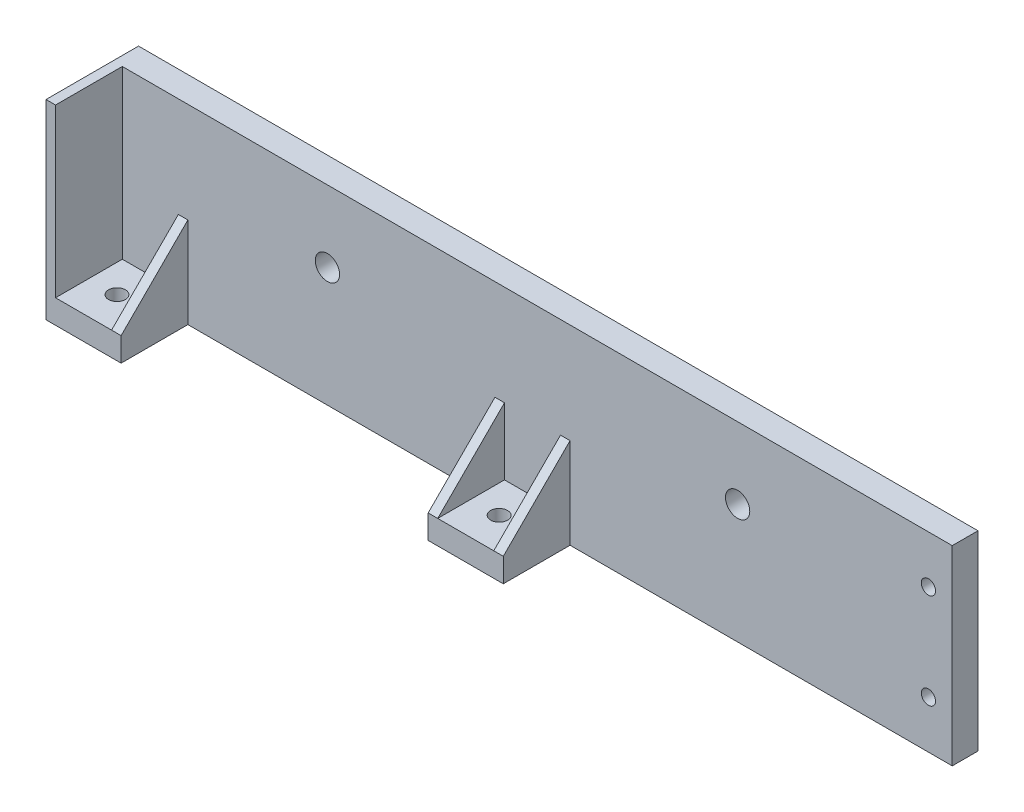
SolidWorks part; units mm, degrees
ref_plane "Front Plane" through (0, 0, 0) normal (0, 0, 1) x (1, 0, 0)
ref_plane "Top Plane" through (0, 0, 0) normal (0, 1, 0) x (1, 0, 0)
ref_plane "Right Plane" through (0, 0, 0) normal (1, 0, 0) x (0, 0, -1)
sketch "Sketch1" plane through (0, 0, 0) normal (0, 0, 1) x (1, 0, 0)
  line L1 (-111.76, -25.4) -> (111.76, -25.4)
  line L2 (-111.76, -25.4) -> (-111.76, 25.4)
  line L3 (-111.76, 25.4) -> (111.76, 25.4)
  line L4 (111.76, -25.4) -> (111.76, 25.4)
  circle A0 centre (-54.61, 6.35) radius 38.1
  circle A1 centre (54.61, 6.35) radius 38.1
  circle A2 centre (-54.61, 6.35) radius 3.2385
  circle A3 centre (54.61, 6.35) radius 3.2385
  point P0 (0, 0)
  dimension "D5" = 76.2
  dimension "D6" = 76.2
  dimension "D7" = 6.477
  dimension "D8" = 6.477
  dimension "D9" = 19.05
  dimension "D3" = 57.15
  dimension "D4" = 57.15
  dimension "D10" = 19.05
  dimension "D1" = 223.52
  dimension "D2" = 50.8
extrude "Boss-Extrude1" add sketch "Sketch1" along normal blind 6.858
sketch "Sketch2" plane through (0, 0, 6.858) normal (0, 0, 1) x (1, 0, 0)
  line L0 (-111.76, -25.4) -> (-91.76, -25.4)
  line L1 (-111.76, -25.4) -> (-111.76, -19.05)
  line L2 (-91.76, -25.4) -> (-91.76, -19.05)
  line L3 (-111.76, -19.05) -> (-91.76, -19.05)
  line L4 (-111.76, -25.4) -> (111.76, -25.4) construction
extrude "Boss-Extrude2" add sketch "Sketch2" along normal blind 17.78
sketch "Sketch3" plane through (0, -19.05, 0) normal (0, 1, 0) x (1, 0, 0)
  circle A0 centre (-101.76, -15.748) radius 2.25
extrude "Cut-Extrude1" cut sketch "Sketch3" against normal blind 17.78
sketch "Sketch4" plane through (0, -19.05, 0) normal (0, 1, 0) x (1, 0, 0)
  line L0 (-111.76, -24.638) -> (-111.76, -6.858)
  line L1 (-111.76, -24.638) -> (-109.22, -24.638)
  line L2 (-111.76, -6.858) -> (-109.22, -6.858)
  line L3 (-109.22, -24.638) -> (-109.22, -6.858)
  line L4 (-91.76, -24.638) -> (-91.76, -6.858)
  line L5 (-91.76, -24.638) -> (-94.3, -24.638)
  line L6 (-91.76, -6.858) -> (-94.3, -6.858)
  line L7 (-94.3, -24.638) -> (-94.3, -6.858)
extrude "Boss-Extrude3" add sketch "Sketch4" along normal blind 17.78
sketch "Sketch6" plane through (-111.76, 0, 0) normal (-1, 0, 0) x (0, 0, 1)
  line L0 (24.638, -1.27) -> (6.858, -1.27)
  line L1 (24.638, -1.27) -> (24.638, -19.05)
  line L4 (24.638, -19.05) -> (6.858, -1.27)
extrude "Cut-Extrude2" cut sketch "Sketch6" against normal up to surface (20 mm away) up to face at (-91.76, -13.335, 15.748)
pattern_linear "LPattern1" count 2 spacing 101.76 along (1, 0, 0) of "Boss-Extrude2", "Cut-Extrude1", "Boss-Extrude3", "Cut-Extrude2"
sketch "Sketch7" plane through (-111.76, 0, 0) normal (-1, 0, 0) x (0, 0, 1)
  line L0 (24.638, -19.05) -> (24.638, 25.4)
  line L1 (6.858, 25.4) -> (24.638, 25.4)
  line L2 (6.858, 25.4) -> (6.858, -1.27)
  line L3 (6.858, -1.27) -> (24.638, -19.05)
extrude "Boss-Extrude4" add sketch "Sketch7" against normal up to surface (2.54 mm away) up to face at (-109.22, -13.1233, 12.7847)
sketch "Sketch8" plane through (0, 0, 0) normal (0, 0, -1) x (-1, 0, 0)
  line L0 (-111.76, -25.4) -> (-111.76, 25.4) construction
  line L1 (-111.76, -25.4) -> (-99.06, -25.4)
  line L2 (-111.76, -25.4) -> (-111.76, 25.4)
  line L3 (-111.76, 25.4) -> (-99.06, 25.4)
  line L4 (-99.06, -25.4) -> (-99.06, 25.4)
  line L5 (111.76, 25.4) -> (-111.76, 25.4) construction
  line L6 (-105.41, 0) -> (-105.41, -25.4)
  line L7 (-111.76, 0) -> (-99.06, 0)
  line L8 (-105.41, 0) -> (-105.41, 25.4)
  point P12 (-105.41, 12.7)
  point P14 (-105.41, -12.7)
  dimension "D1" = 12.7
hole_wizard "CSK for #6 Flat Head Machine Screw1" positions "Sketch9" profile "Sketch10" countersink size "#6" standard "ANSI Inch" end condition through all
sketch "Sketch9" plane through (0, 0, 0) normal (0, 0, -1) x (-1, 0, 0)
  point P0 (-105.41, 12.7)
  point P2 (-105.41, -12.7)
sketch "Sketch10" plane through (105.41, 12.7, 0) normal (1, 0, 0) x (0, 1, 0)
  line L0 (0, 0) -> (0, 24.638)
  line L1 (0, 24.638) -> (1.8986, 24.638)
  line L2 (1.8986, 24.638) -> (1.8986, 2.3999)
  line L3 (1.8986, 2.3999) -> (3.9849, 0)
  line L5 (3.9849, 0) -> (0, 0)
  line L6 (-1.8986, 2.3999) -> (-3.9849, 0) construction
  line L11 (0, -6.35) -> (0, 107.95) construction
  dimension "Thru Hole Dia." = 3.7973
  dimension "Thru Hole Depth" = 24.638
  dimension "Near C'Sink Dia." = 7.9698
  dimension "Near C'Sink Angle" = 82
